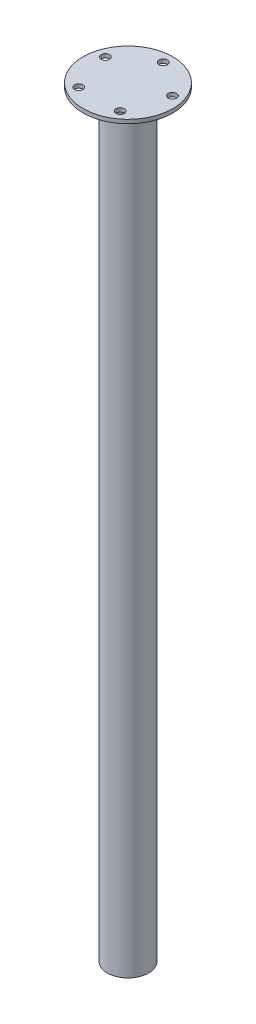
SolidWorks part; units mm, degrees
ref_plane "Front Plane" through (0, 0, 0) normal (0, 0, 1) x (1, 0, 0)
ref_plane "Top Plane" through (0, 0, 0) normal (0, 1, 0) x (1, 0, 0)
ref_plane "Right Plane" through (0, 0, 0) normal (1, 0, 0) x (0, 0, -1)
sketch "Sketch1" plane through (0, 0, 0) normal (0, 1, 0) x (1, 0, 0)
  circle A0 centre (0, 0) radius 16
  circle A1 centre (0, 0) radius 14
  dimension "D1" = 32
  dimension "D2" = 28
extrude "Boss-Extrude1" add sketch "Sketch1" along normal blind 590
sketch "Sketch2" plane through (0, 590, 0) normal (0, 1, 0) x (1, 0, 0)
  circle A0 centre (0, 0) radius 35
  dimension "D1" = 70
extrude "Boss-Extrude2" add sketch "Sketch2" along normal blind 3
chamfer "Chamfer1" distance 2 angle 45 1 edges at (0, 590, 16)
sketch "Sketch4" plane through (0, 593, 0) normal (0, 1, 0) x (1, 0, 0)
  circle A0 centre (0, 0) radius 27.5 construction
  circle A1 centre (0, 27.5) radius 3.25
  circle A2 centre (26.1541, 8.498) radius 3.25
  circle A3 centre (16.1641, -22.248) radius 3.25
  circle A4 centre (-16.1641, -22.248) radius 3.25
  circle A5 centre (-26.1541, 8.498) radius 3.25
  point P15 (0, 0)
  dimension "D1" = 55
  dimension "D2" = 6.5
  dimension "D3" = 5
extrude "Cut-Extrude2" cut sketch "Sketch4" against normal through all
